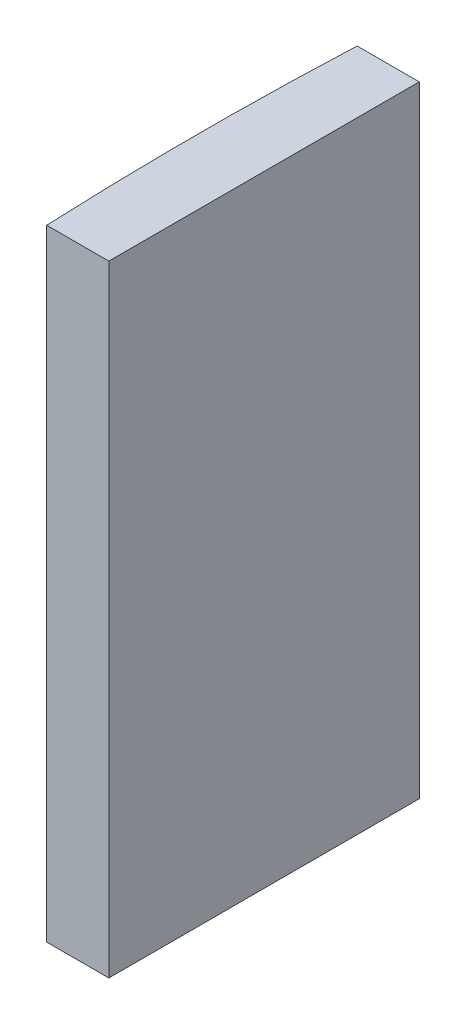
SolidWorks part; units mm, degrees
ref_plane "前视基准面" through (0, 0, 0) normal (0, 0, 1) x (1, 0, 0)
ref_plane "上视基准面" through (0, 0, 0) normal (0, 1, 0) x (1, 0, 0)
ref_plane "右视基准面" through (0, 0, 0) normal (1, 0, 0) x (0, 0, -1)
sketch "草图1" plane through (0, 0, 0) normal (0, 1, 0) x (1, 0, 0)
  line L0 (-137.6835, 0) -> (10.8051, 0) construction
  line L1 (-110.1557, 5) -> (-108.1548, 5)
  line L2 (-110.1557, -5) -> (-108.1548, -5)
  line L3 (-108.1548, 5) -> (-108.1548, -5)
  arc A0 (-110.1557, 5) -> (-110.1557, -5) centre (4.3552, 0) ccw
  point P2 (-110.2648, 0)
  point P4 (-108.1548, 0)
  dimension "D2" = 5
  dimension "D3" = 114.62
  dimension "D4" = 2.11
  dimension "D1" = 5
extrude "凸台-拉伸1" add sketch "草图1" along normal blind 20
